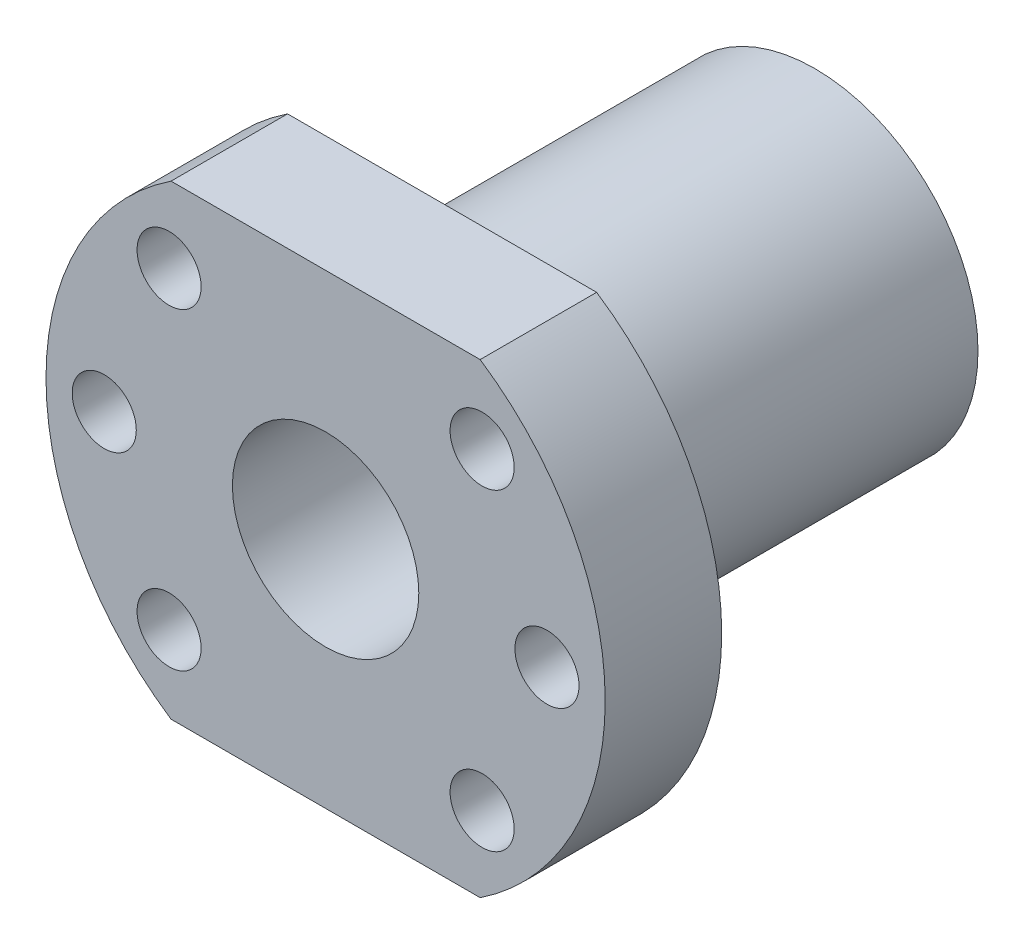
SolidWorks part; units mm, degrees
material "1.4310 (X10CrNi18-8)"
ref_plane "Front Plane" through (0, 0, 0) normal (0, 0, 1) x (1, 0, 0)
ref_plane "Top Plane" through (0, 0, 0) normal (0, 1, 0) x (1, 0, 0)
ref_plane "Right Plane" through (0, 0, 0) normal (1, 0, 0) x (0, 0, -1)
sketch "Sketch1" plane through (0, 0, 0) normal (0, 0, 1) x (1, 0, 0)
  circle A0 centre (0, 0) radius 8
  circle A1 centre (0, 0) radius 14
  dimension "D1" = 16
  dimension "D2" = 28
extrude "Boss-Extrude1" add sketch "Sketch1" against normal blind 42
sketch "Sketch2" plane through (0, 0, 0) normal (0, 0, 1) x (1, 0, 0)
  line L0 (-13.2665, 20) -> (13.2665, 20)
  line L1 (-13.2665, -20) -> (13.2665, -20)
  circle A0 centre (0, 0) radius 24
  circle A1 centre (0, 0) radius 8 construction
  circle A2 centre (0, 0) radius 8
  dimension "D1" = 48
  dimension "D2" = 40
  dimension "D3" = 20
extrude "Boss-Extrude2" add sketch "Sketch2" against normal blind 10 contours L0 A0 L1
hole_wizard "M5 Clearance Hole1" positions "Sketch3" profile "Sketch4" hole size "M5" standard "ANSI Metric" end condition through all
sketch "Sketch3" plane through (0, 0, 0) normal (0, 0, 1) x (1, 0, 0)
  line L0 (13.435, -13.435) -> (-13.435, 13.435) construction
  line L2 (-13.435, -13.435) -> (13.435, 13.435) construction
  circle A0 centre (0, 0) radius 19 construction
  point P8 (-13.435, 13.435)
  point P23 (13.435, -13.435)
  point P24 (0, 0)
  point P28 (13.435, 13.435)
  point P45 (-13.435, -13.435)
  point P46 (0, 0)
  point P48 (19, 0)
  point P50 (-19, 0)
  dimension "D1" = 38
  dimension "D2" = 45
  dimension "D3" = 90
sketch "Sketch4" plane through (-19, 0, 0) normal (1, 0, 0) x (0, -1, 0)
  line L0 (0, 0) -> (0, 42)
  line L1 (0, 42) -> (2.75, 42)
  line L2 (2.75, 42) -> (2.75, 0)
  line L5 (2.75, 0) -> (0, 0)
  line L11 (0, -6.35) -> (0, 107.95) construction
  dimension "Thru Hole Dia." = 5.5
  dimension "Thru Hole Depth" = 42
